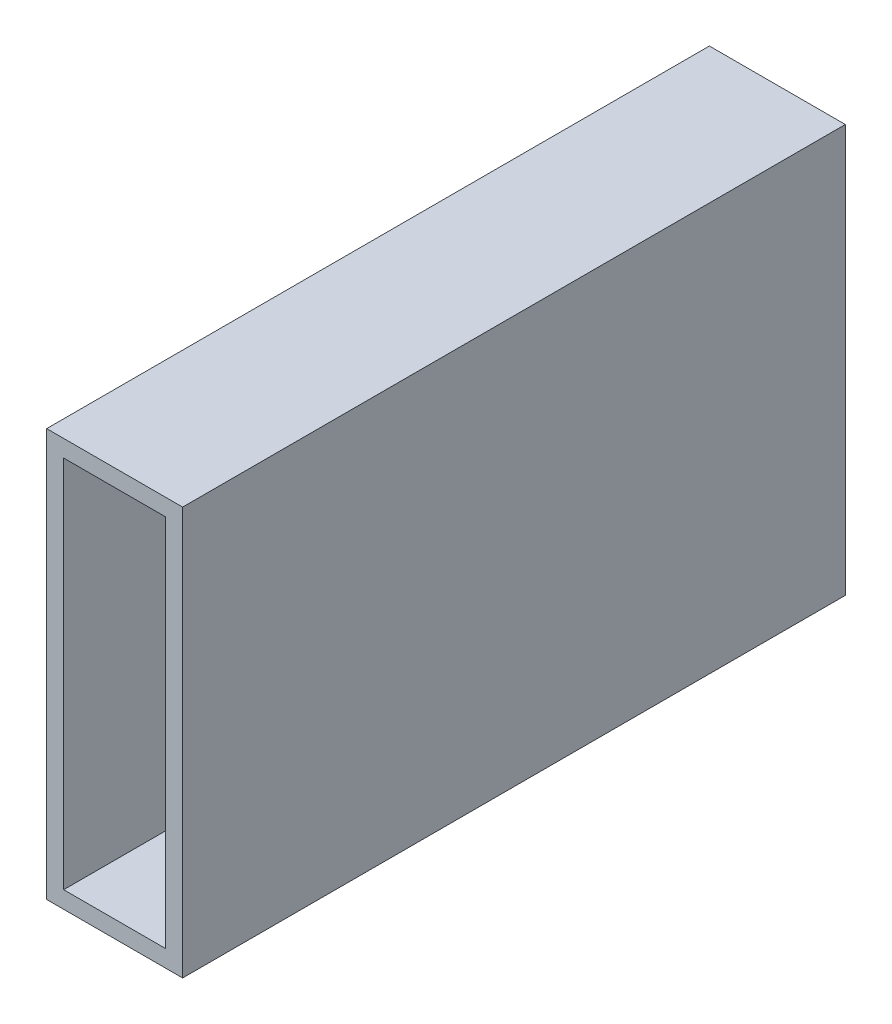
SolidWorks part; units mm, degrees
ref_plane "Front Plane" through (0, 0, 0) normal (0, 0, 1) x (1, 0, 0)
ref_plane "Top Plane" through (0, 0, 0) normal (0, 1, 0) x (1, 0, 0)
ref_plane "Right Plane" through (0, 0, 0) normal (1, 0, 0) x (0, 0, -1)
sketch "Sketch1" plane through (0, 0, 0) normal (0, 0, 1) x (1, 0, 0)
  line L1 (-12.7, -38.1) -> (12.7, -38.1)
  line L2 (-12.7, -38.1) -> (-12.7, 38.1)
  line L3 (-12.7, 38.1) -> (12.7, 38.1)
  line L4 (12.7, -38.1) -> (12.7, 38.1)
  line L5 (-12.7, -38.1) -> (12.7, 38.1) construction
  line L6 (-12.7, 38.1) -> (12.7, -38.1) construction
  point P0 (0, 0)
  dimension "D1" = 25.4
  dimension "D2" = 76.2
extrude "Boss-Extrude1" add sketch "Sketch1" along normal mid plane 123.825
shell "Shell1" thickness 3.175
